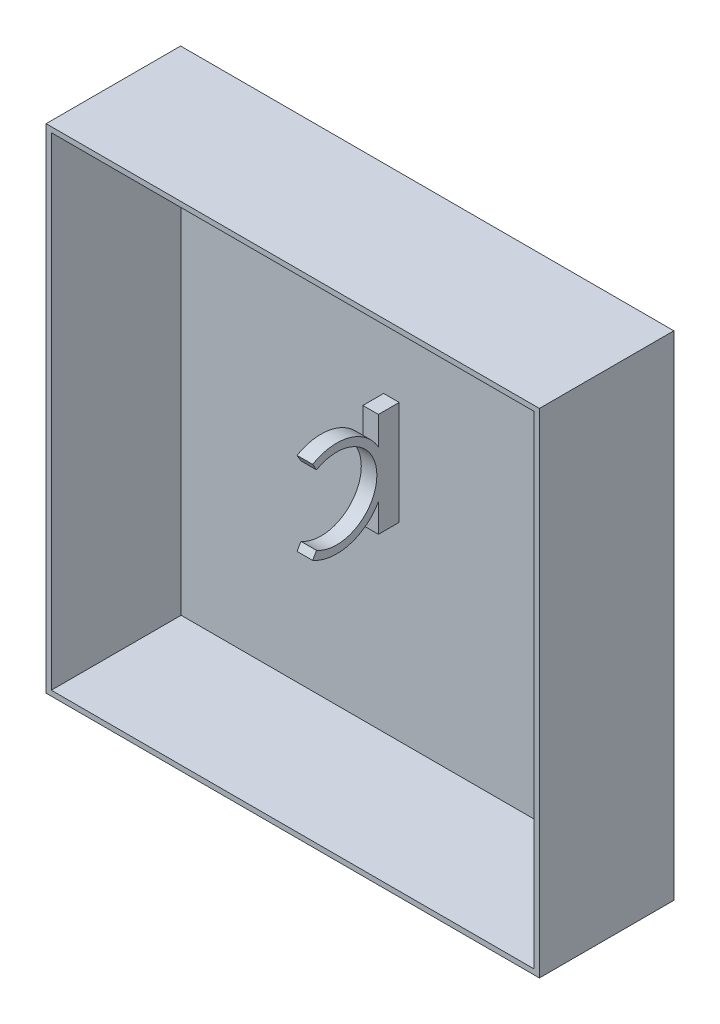
SolidWorks part; units mm, degrees
ref_plane "Alzado" through (0, 0, 0) normal (0, 0, 1) x (1, 0, 0)
ref_plane "Planta" through (0, 0, 0) normal (0, 1, 0) x (1, 0, 0)
ref_plane "Vista lateral" through (0, 0, 0) normal (1, 0, 0) x (0, 0, -1)
sketch "Croquis1" plane through (0, 0, 0) normal (0, 0, 1) x (1, 0, 0)
  line L0 (-42.5, 35.9765) -> (-42.5, 39.9765) construction
  line L1 (47.5, -47.5) -> (-47.5, -47.5)
  line L2 (47.5, -47.5) -> (47.5, 47.5)
  line L3 (47.5, 47.5) -> (-47.5, 47.5)
  line L4 (-47.5, -47.5) -> (-47.5, 47.5)
  line L5 (47.5, -47.5) -> (-47.5, 47.5) construction
  line L6 (47.5, 47.5) -> (-47.5, -47.5) construction
  line L7 (0, 0) -> (0, -47.5) construction
  line L8 (-44.5, 39.9765) -> (-44.5, 34.9765)
  line L9 (-40.5, 39.9765) -> (-40.5, 34.9765)
  line L10 (40.5, 39.9765) -> (40.5, 34.9765)
  line L11 (44.5, 39.9765) -> (44.5, 34.9765)
  line L12 (0, 0) -> (-40, 0) construction
  circle A0 centre (0, 0) radius 38 construction
  arc A1 (-44.5, 34.9765) -> (-40.5, 34.9765) centre (-42.5, 33.4765) ccw
  arc A2 (-40.5, 39.9765) -> (-44.5, 39.9765) centre (-42.5, 39.9765) ccw
  arc A3 (40.5, 39.9765) -> (44.5, 39.9765) centre (42.5, 39.9765) cw
  arc A4 (44.5, 34.9765) -> (40.5, 34.9765) centre (42.5, 33.4765) cw
  point P0 (0, 0)
  dimension "D3" = 76
  dimension "D4" = 5
  dimension "D1" = 95
  dimension "D5" = 5
  dimension "D6" = 5
  dimension "D7" = 40
extrude "Saliente-Extruir1" add sketch "Croquis1" along normal blind 0.9
sketch "Croquis2" plane through (0, 0, 0.9) normal (0, 0, 1) x (1, 0, 0)
  line L4 (-46.5, 46.5) -> (-46.5, -46.5)
  line L5 (-46.5, -46.5) -> (46.5, -46.5)
  line L6 (46.5, -46.5) -> (46.5, 46.5)
  line L7 (46.5, 46.5) -> (-46.5, 46.5)
  line L8 (-47.5, 47.5) -> (-47.5, -47.5)
  line L9 (-47.5, -47.5) -> (47.5, -47.5)
  line L10 (47.5, -47.5) -> (47.5, 47.5)
  line L11 (47.5, 47.5) -> (-47.5, 47.5)
  line L12 (-47.5, 47.5) -> (-47.5, -47.5)
  line L13 (-47.5, -47.5) -> (47.5, -47.5)
  line L14 (47.5, -47.5) -> (47.5, 47.5)
  line L15 (47.5, 47.5) -> (-47.5, 47.5)
  dimension "D1" = 0
  dimension "D2" = 1
extrude "Saliente-Extruir2" add sketch "Croquis2" along normal blind 25
sketch "Croquis3" plane through (0, 0, 0.9) normal (0, 0, 1) x (1, 0, 0)
  line L0 (0, 0) -> (-40, 0) construction
  line L2 (-7.5, 10) -> (-4.5, 10)
  line L3 (-7.5, 10) -> (-7.5, -10)
  line L4 (-7.5, -10) -> (-4.5, -10)
  line L5 (-4.5, 10) -> (-4.5, -10)
  point P7 (-7.5, 0)
  point P8 (-6, 10)
  dimension "D1" = 40
  dimension "D2" = 34
  dimension "D3" = 3
  dimension "D4" = 20
extrude "Saliente-Extruir3" add sketch "Croquis3" along normal blind 4
sketch "Croquis4" plane through (-7.5, 0, 0) normal (-1, 0, 0) x (0, 0, 1)
  line L0 (4.9, 0) -> (12.95, 0) construction
  line L1 (4.9, 10) -> (4.9, -10) construction
  line L2 (12.95, 0) -> (17.575, 8.0107) construction
  line L3 (12.95, 0) -> (17.575, -8.0107) construction
  line L4 (17.575, 8.0107) -> (16.825, 6.7117)
  line L5 (17.575, -8.0107) -> (16.825, -6.7117)
  line L6 (4.9, -4.5563) -> (4.9, 4.5563)
  arc A0 (16.825, 6.7117) -> (16.825, -6.7117) centre (12.95, 0) ccw
  arc A1 (17.575, 8.0107) -> (4.9, 4.5563) centre (12.95, 0) ccw
  arc A2 (4.9, -4.5563) -> (17.575, -8.0107) centre (12.95, 0) ccw
  circle A3 centre (12.95, 0) radius 7.75 construction
  circle A4 centre (12.95, 0) radius 9.25 construction
  point P5 (22.2, 0)
  point P10 (20.3614, 2.2659)
  dimension "D2" = 15.5
  dimension "D1" = 8.05
  dimension "D4" = 30
  dimension "D3" = 1.5
extrude "Saliente-Extruir4" add sketch "Croquis4" against normal up to vertex
